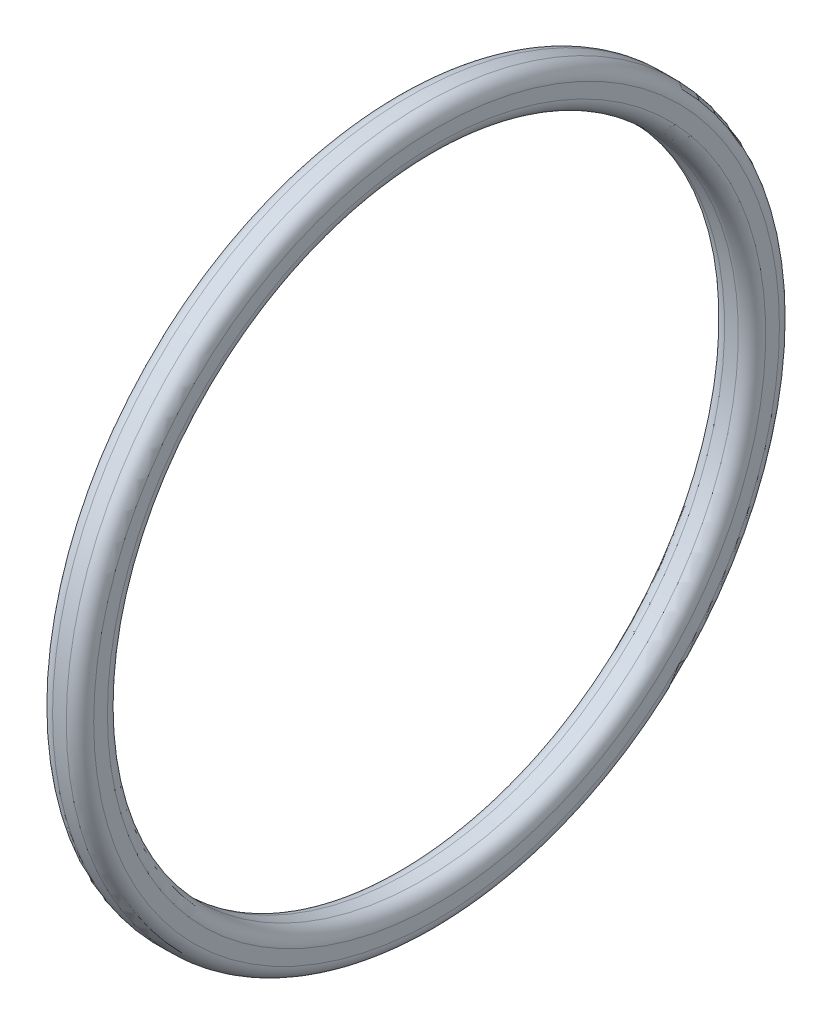
SolidWorks part; units mm, degrees
ref_plane "Face" through (0, 0, 0) normal (0, 0, 1) x (1, 0, 0)
ref_plane "Dessus" through (0, 0, 0) normal (0, 1, 0) x (1, 0, 0)
ref_plane "Droite" through (0, 0, 0) normal (1, 0, 0) x (0, 0, -1)
sketch "Esquisse1" plane through (0, 0, 0) normal (0, 0, 1) x (1, 0, 0)
  line L0 (-12.332, 0) -> (13.4044, 0) construction
  line L2 (0.5, 11.5) -> (1, 11.5)
  line L3 (0, 12) -> (0, 12.5)
  line L4 (0.5, 13) -> (1, 13)
  line L5 (1.5, 12) -> (1.5, 12.5)
  arc A0 (1.5, 12) -> (1, 11.5) centre (1, 12) cw
  arc A1 (1.5, 12.5) -> (1, 13) centre (1, 12.5) ccw
  arc A2 (0.5, 13) -> (0, 12.5) centre (0.5, 12.5) ccw
  arc A3 (0, 12) -> (0.5, 11.5) centre (0.5, 12) ccw
  dimension "D3" = 0.5
  dimension "D1" = 1.5
  dimension "D2" = 1.5
  dimension "D4" = 13
revolve "Base-Révolution" add sketch "Esquisse1" angle 360 about L0
